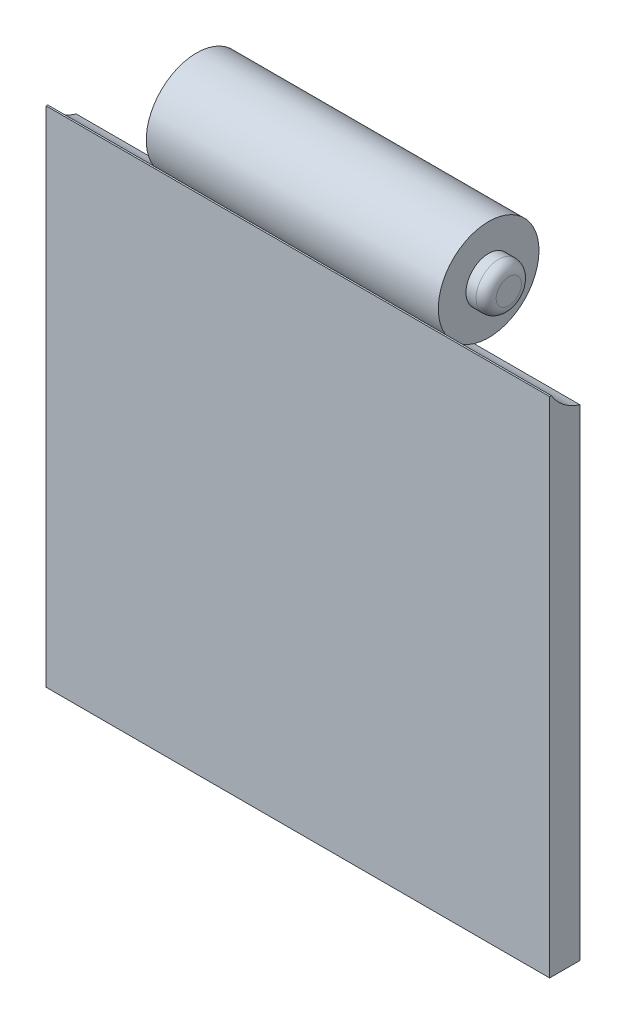
SolidWorks part; units mm, degrees
ref_plane "Front Plane" through (0, 0, 0) normal (0, 0, 1) x (1, 0, 0)
ref_plane "Top Plane" through (0, 0, 0) normal (0, 1, 0) x (1, 0, 0)
ref_plane "Right Plane" through (0, 0, 0) normal (1, 0, 0) x (0, 0, -1)
sketch "Sketch1" plane through (0, 0, 0) normal (0, 1, 0) x (1, 0, 0)
  line L1 (-25, 1.5) -> (25, 1.5)
  line L2 (-25, 1.5) -> (-25, -1.5)
  line L3 (-25, -1.5) -> (25, -1.5)
  line L4 (25, 1.5) -> (25, -1.5)
  line L5 (-25, 1.5) -> (25, -1.5) construction
  line L6 (-25, -1.5) -> (25, 1.5) construction
  point P0 (0, 0)
  dimension "D1" = 3
  dimension "D2" = 50
extrude "Boss-Extrude1" add sketch "Sketch1" along normal blind 50
sketch "Sketch2" plane through (0, 0, 0) normal (1, 0, 0) x (0, 0, -1)
  circle A0 centre (2.9404, 52.5895) radius 5
extrude "Boss-Extrude2" add sketch "Sketch2" along normal blind 14.5 and the other way blind 14.5
sketch "Sketch3" plane through (14.5, 0, 0) normal (1, 0, 0) x (0, 0, -1)
  circle A0 centre (2.9404, 52.5895) radius 2.25
extrude "Boss-Extrude3" add sketch "Sketch3" along normal blind 2
fillet "Fillet2" radius 1 1 edges at (16.5, 52.5895, -5.1904)
mirror "Mirror1" about plane through (0, 0, 0) normal (1, 0, 0) of "Boss-Extrude3", "Fillet2"
sketch "Sketch4" plane through (14.5, 0, 0) normal (1, 0, 0) x (0, 0, -1)
  line L2 (1.5, 50) -> (1.5, 47.8014)
  line L3 (-1.3369, 50) -> (1.5, 50)
  line L4 (1.5, 50) -> (1.5, 47.8014)
  line L5 (-1.3369, 50) -> (1.5, 50)
  arc A0 (-1.3369, 50) -> (1.5, 47.8014) centre (2.9404, 52.5895) ccw
  arc A1 (1.5, 47.8014) -> (-1.3369, 50) centre (2.9404, 52.5895) ccw
  dimension "D1" = 0
extrude "Cut-Extrude1" cut sketch "Sketch4" along normal through all
mirror "Mirror2" about plane through (0, 0, 0) normal (1, 0, 0) of "Cut-Extrude1"
